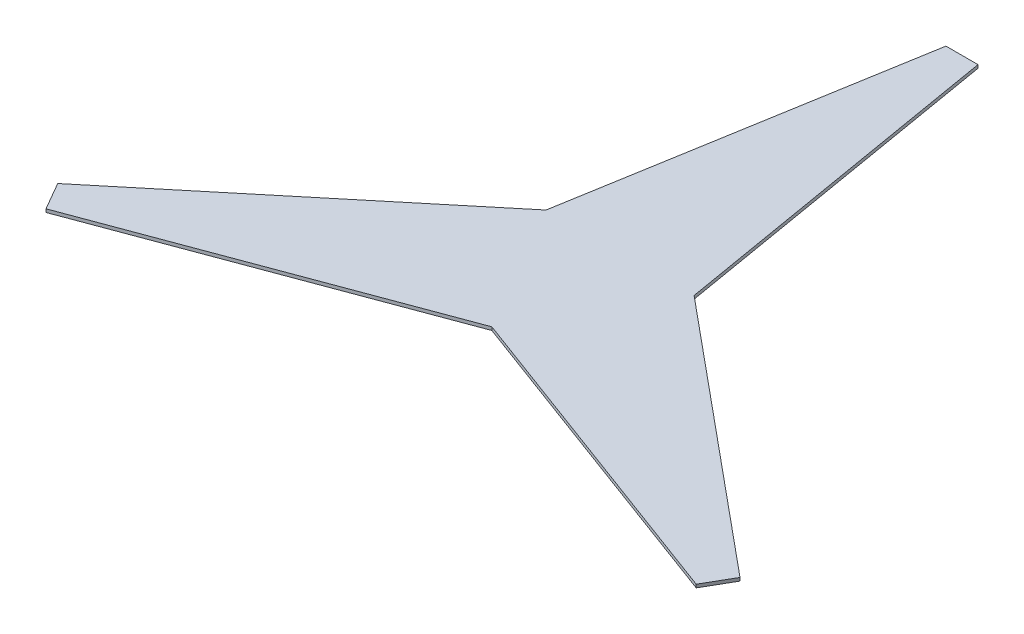
SolidWorks part; units mm, degrees
ref_plane "Alzado" through (0, 0, 0) normal (0, 0, 1) x (1, 0, 0)
ref_plane "Planta" through (0, 0, 0) normal (0, 1, 0) x (1, 0, 0)
ref_plane "Vista lateral" through (0, 0, 0) normal (1, 0, 0) x (0, 0, -1)
sketch "Croquis1" plane through (0, 0, 0) normal (0, 1, 0) x (1, 0, 0)
  line L0 (0, 0) -> (0, 1200) construction
  line L1 (1064.2305, -556.6987) -> (230.9516, 133.34)
  line L2 (1014.2305, -643.3013) -> (0, -266.68)
  line L6 (-50, 1200) -> (-230.9516, 133.34)
  line L7 (50, 1200) -> (230.9516, 133.34)
  line L9 (-1014.2305, -643.3013) -> (0, -266.68)
  line L10 (-1064.2305, -556.6987) -> (-230.9516, 133.34)
  line L11 (-50, 1200) -> (50, 1200)
  line L12 (1064.2305, -556.6987) -> (1014.2305, -643.3013)
  line L13 (-1064.2305, -556.6987) -> (-1014.2305, -643.3013)
  circle A0 centre (0, 0) radius 1250 construction
  point P17 (0, 0)
  point P20 (0, 1200)
  dimension "D1" = 2500
  dimension "D2" = 3
extrude "Saliente-Extruir2" add sketch "Croquis1" along normal blind 10
sketch "Croquis2" plane through (0, 10, 0) normal (0, 1, 0) x (1, 0, 0)
  circle A0 centre (0, 0) radius 187.5
  dimension "D1" = 375
sketch "Croquis3" plane through (0, 10, 0) normal (0, 1, 0) x (1, 0, 0)
  line L0 (-50, 1200) -> (-85.7035, 989.5379)
  line L1 (-50, 1200) -> (-230.9516, 133.34) construction
  line L2 (-85.7035, 989.5379) -> (85.7035, 989.5379)
  line L3 (230.9516, 133.34) -> (50, 1200) construction
  line L4 (85.7035, 989.5379) -> (50, 1200)
  line L5 (50, 1200) -> (-50, 1200)
  line L6 (0, 1200) -> (0, 989.5379) construction
